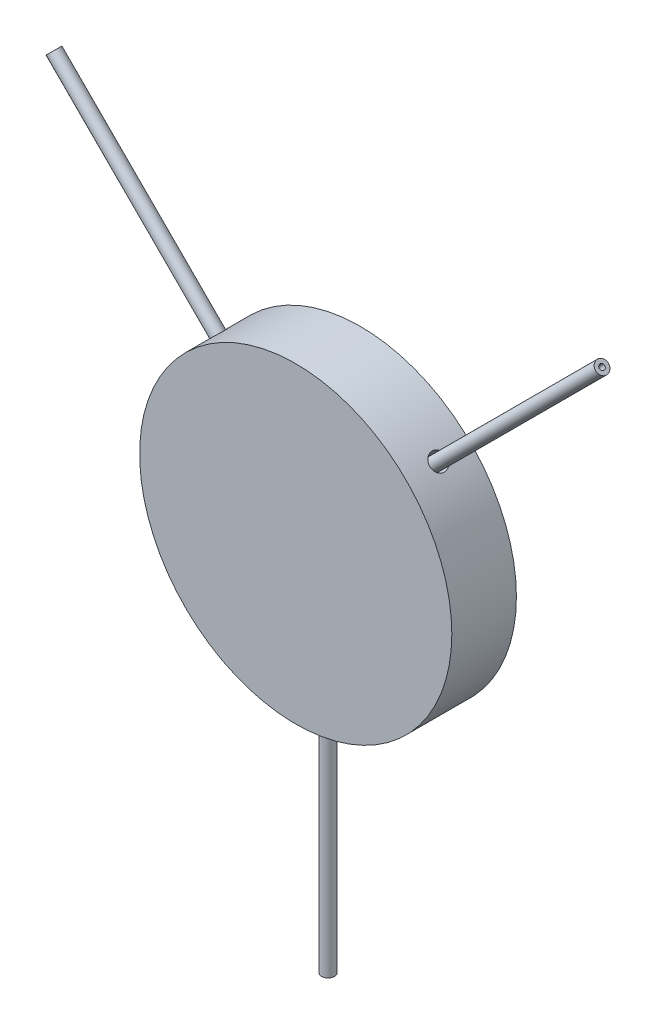
SolidWorks part; units mm, degrees
other "Junction"
other "InletNeedle1"
other "InletNeedle2"
other "OutletNeedle" parameters "D1"=3, "D2"=2.7125
ref_plane "Front Plane" through (0, 0, 0) normal (0, 0, 1) x (1, 0, 0)
ref_plane "Top Plane" through (0, 0, 0) normal (0, 1, 0) x (1, 0, 0)
ref_plane "Right Plane" through (0, 0, 0) normal (1, 0, 0) x (0, 0, -1)
sketch "Sketch1" plane through (0, 0, 0) normal (0, 0, 1) x (1, 0, 0)
  circle A0 centre (0, 0) radius 7.25
  dimension "D1" = 14.5
extrude "Boss-Extrude1" add sketch "Sketch1" along normal blind 3
sketch "Sketch2" plane through (0, 0, 0) normal (0, 1, 0) x (1, 0, 0)
  circle A0 centre (0, -1.5) radius 0.4
  dimension "D1" = 0.8
extrude "Cut-Extrude1" cut sketch "Sketch2" against normal up to surface (7.25 mm away)
ref_plane "Plane1" through (0, 0, 0) normal (-0.7071, 0.7071, 0) x (0.7071, 0.7071, 0)
sketch "Sketch3" plane through (0, 0, 0) normal (-0.7071, 0.7071, 0) x (0.7071, 0.7071, 0)
  line L0 (7.25, -1.5) -> (-7.25, -1.5) construction
  line L1 (7.25, -3) -> (7.25, 0) construction
  line L2 (-7.25, 0) -> (-7.25, -3) construction
  circle A0 centre (0, -1.5) radius 0.4
  dimension "D1" = 0.8
extrude "Cut-Extrude2" cut sketch "Sketch3" along normal up to surface (7.239 mm away)
ref_plane "Plane2" through (0, 0, 0) normal (0.7071, 0.7071, 0) x (0.7071, -0.7071, 0)
sketch "Sketch4" plane through (0, 0, 0) normal (0.7071, 0.7071, 0) x (0.7071, -0.7071, 0)
  line L0 (0, 0) -> (0, -3.0044) construction
  circle A0 centre (0, -1.5022) radius 0.4
  dimension "D1" = 0.8
extrude "Cut-Extrude3" cut sketch "Sketch4" along normal up to surface (7.239 mm away)
sketch "Sketch5" plane through (0, 0, 0) normal (0.7071, 0.7071, 0) x (0.7071, -0.7071, 0)
  circle A0 centre (0, -1.5022) radius 0.125
  circle A1 centre (0, -1.5022) radius 0.3
  dimension "D1" = 0.25
  dimension "D2" = 0.6
extrude "Boss-Extrude2" add sketch "Sketch5" along normal blind 13 from offset 5 separate body
sketch "Sketch6" plane through (0, 0, 0) normal (-0.7071, 0.7071, 0) x (0.7071, 0.7071, 0)
  circle A0 centre (0, -1.5) radius 0.125
  circle A1 centre (0, -1.5) radius 0.3
  dimension "D1" = 0.25
  dimension "D2" = 0.6
extrude "Boss-Extrude3" add sketch "Sketch6" along normal blind 13 from offset 5 separate body
sketch "Sketch7" plane through (0, 0, 0) normal (0, 1, 0) x (1, 0, 0)
  circle A0 centre (0, -1.5) radius 0.125
  circle A1 centre (0, -1.5) radius 0.3
  dimension "D1" = 0.25
  dimension "D2" = 0.6
extrude "Boss-Extrude4" add sketch "Sketch7" against normal blind 13 from offset 5 separate body
equation "\"junctionDiam\"= 14.5"
equation "\"needleOD\"= 0.6"
equation "\"needleID\"= 0.25"
equation "\"needleLength\"= 13"
equation "\"channelDiam\"= 0.8"
equation "\"junctionThickness\"= 3"
equation "\"D1@Boss-Extrude1\"=\"junctionThickness\""
equation "\"D1@Sketch2\"=\"channelDiam\""
equation "\"D1@Sketch3\"=\"channelDiam\""
equation "\"D1@Sketch5\"=\"needleID\""
equation "\"D2@Sketch5\"=\"needleOD\""
equation "\"D1@Boss-Extrude2\"=\"needleLength\""
equation "\"needleOffset\"=5"
equation "\"D19@Boss-Extrude2\"=\"needleOffset\""
equation "\"D1@Sketch6\"=\"needleID\""
equation "\"D2@Sketch6\"=\"needleOD\""
equation "\"D1@Boss-Extrude3\"=\"needleLength\""
equation "\"D19@Boss-Extrude3\"=\"needleOffset\""
equation "\"D1@Sketch7\"=\"needleID\""
equation "\"D2@Sketch7\"=\"needleOD\""
equation "\"D1@Boss-Extrude4\"=\"needleLength\""
equation "\"D19@Boss-Extrude4\"=\"needleOffset\""
